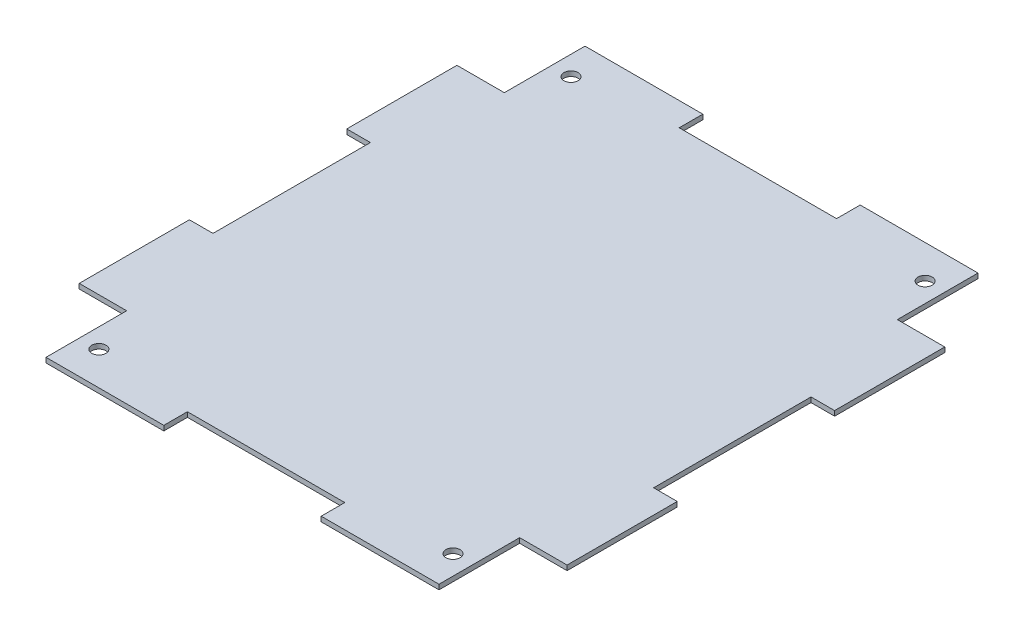
SolidWorks part; units mm, degrees
ref_plane "Front Plane" through (0, 0, 0) normal (0, 0, 1) x (1, 0, 0)
ref_plane "Top Plane" through (0, 0, 0) normal (0, 1, 0) x (1, 0, 0)
ref_plane "Right Plane" through (0, 0, 0) normal (1, 0, 0) x (0, 0, -1)
sketch "Sketch1" plane through (0, 0, 0) normal (0, 1, 0) x (1, 0, 0)
  line L0 (-25.4, 86.995) -> (-63.4314, 86.995)
  line L1 (-88.9, -101.6) -> (88.9, -101.6) construction
  line L2 (101.6, -88.9) -> (101.6, 88.9) construction
  line L3 (88.9, 101.6) -> (-88.9, 101.6) construction
  line L4 (-78.74, -60.96) -> (-63.4314, -60.96)
  line L5 (-63.4314, -60.96) -> (-63.4314, -86.995)
  line L6 (-63.4314, -86.995) -> (-25.4, -86.995)
  line L7 (63.4314, -86.995) -> (63.4314, -60.96)
  line L8 (63.4314, -60.96) -> (78.74, -60.96)
  line L9 (78.74, -60.96) -> (78.74, -25.4)
  line L10 (78.74, 60.96) -> (63.4314, 60.96)
  line L11 (63.4314, 60.96) -> (63.4314, 86.995)
  line L12 (63.4314, 86.995) -> (25.4, 86.995)
  line L13 (-63.4314, 86.995) -> (-63.4314, 60.96)
  line L14 (-63.4314, 60.96) -> (-78.74, 60.96)
  line L15 (-78.74, 60.96) -> (-78.74, 25.4)
  line L16 (-78.74, -25.4) -> (-78.74, -60.96)
  line L17 (-78.74, -25.4) -> (-71.12, -25.4)
  line L19 (-78.74, 25.4) -> (-71.12, 25.4)
  line L20 (-71.12, -25.4) -> (-71.12, 25.4)
  line L22 (-25.4, 86.995) -> (-25.4, 79.375)
  line L23 (-25.4, 79.375) -> (25.4, 79.375)
  line L24 (25.4, 86.995) -> (25.4, 79.375)
  line L25 (78.74, 25.4) -> (71.12, 25.4)
  line L27 (78.74, -25.4) -> (71.12, -25.4)
  line L28 (71.12, 25.4) -> (71.12, -25.4)
  line L30 (25.4, -86.995) -> (25.4, -79.375)
  line L31 (25.4, -79.375) -> (-25.4, -79.375)
  line L32 (-25.4, -86.995) -> (-25.4, -79.375)
  line L33 (78.74, 25.4) -> (78.74, 60.96)
  line L34 (25.4, -86.995) -> (63.4314, -86.995)
  line L35 (-101.6, 88.9) -> (-101.6, -88.9) construction
  arc A0 (88.9, -101.6) -> (101.6, -88.9) centre (88.9, -88.9) ccw construction
  arc A1 (-101.6, -88.9) -> (-88.9, -101.6) centre (-88.9, -88.9) ccw construction
  arc A2 (101.6, 88.9) -> (88.9, 101.6) centre (88.9, 88.9) ccw construction
  arc A3 (-101.6, 88.9) -> (-88.9, 101.6) centre (-88.9, 88.9) cw construction
  circle A4 centre (-57.15, 76.2) radius 2.286
  circle A5 centre (57.15, 76.2) radius 2.286
  circle A6 centre (57.15, -76.2) radius 2.286
  circle A7 centre (-57.15, -76.2) radius 2.286
  point P3 (0, 101.6)
  point P5 (101.6, 0)
  point P13 (101.6, 101.6)
  point P16 (-101.6, 101.6)
  point P38 (-71.12, 0)
  point P55 (0, -79.375)
  point P56 (0, 79.375)
  point P57 (71.12, 0)
  dimension "D2" = 12.7
  dimension "D11" = 4.572
  dimension "D8" = 44.45
  dimension "D1" = 203.2
  dimension "D3" = 203.2
  dimension "D4" = 22.86
  dimension "D5" = 15.3086
  dimension "D6" = 35.56
  dimension "D7" = 173.99
  dimension "D12" = 50.8
  dimension "D13" = 25.4
  dimension "D14" = 44.45
  dimension "D15" = 25.4
  dimension "D18" = 7.62
extrude "Main Body" add sketch "Sketch1" along normal blind 1.5875
sketch "Sketch2" plane through (0, 1.5875, 0) normal (0, 1, 0) x (1, 0, 0)
  line L0 (0, -1000) -> (0, 49000) construction
  line L1 (-1000, 0) -> (49000, 0) construction
  line L2 (-78.74, -60.96) -> (-63.4314, -60.96) construction
  line L3 (-71.12, -25.4) -> (-78.74, -25.4) construction
  line L4 (-78.74, -25.4) -> (-78.74, -60.96) construction
  circle A0 centre (-73.66, -30.48) radius 2.286
  circle A1 centre (-73.66, -55.88) radius 2.286
  circle A2 centre (73.66, -55.88) radius 2.286
  circle A3 centre (73.66, -30.48) radius 2.286
  circle A4 centre (73.66, 30.48) radius 2.286
  circle A5 centre (73.66, 55.88) radius 2.286
  circle A6 centre (-73.66, 55.88) radius 2.286
  circle A7 centre (-73.66, 30.48) radius 2.286
  dimension "D1" = 4.572
  dimension "D2" = 5.08
  dimension "D3" = 5.08
  dimension "D4" = 5.08
sketch "Sketch3" plane through (0, 1.5875, 0) normal (0, 1, 0) x (1, 0, 0)
  line L1 (-50.8, 63.5) -> (50.8, 63.5) construction
  line L2 (-50.8, 63.5) -> (-50.8, -63.5) construction
  line L3 (-50.8, -63.5) -> (50.8, -63.5) construction
  line L4 (50.8, 63.5) -> (50.8, -63.5) construction
  circle A0 centre (46.99, -59.69) radius 1.5875
  circle A1 centre (-46.99, -59.69) radius 1.5875
  circle A2 centre (-46.99, 59.69) radius 1.5875
  circle A3 centre (46.99, 59.69) radius 1.5875
  point P5 (50.8, 0)
  point P7 (0, 63.5)
  dimension "D3" = 3.81
  dimension "D4" = 3.81
  dimension "D5" = 3.175
  dimension "D8" = 3.81
  dimension "D9" = 3.81
  dimension "D10" = 3.81
  dimension "D1" = 101.6
  dimension "D2" = 127
  dimension "D6" = 2
  dimension "D7" = 2
